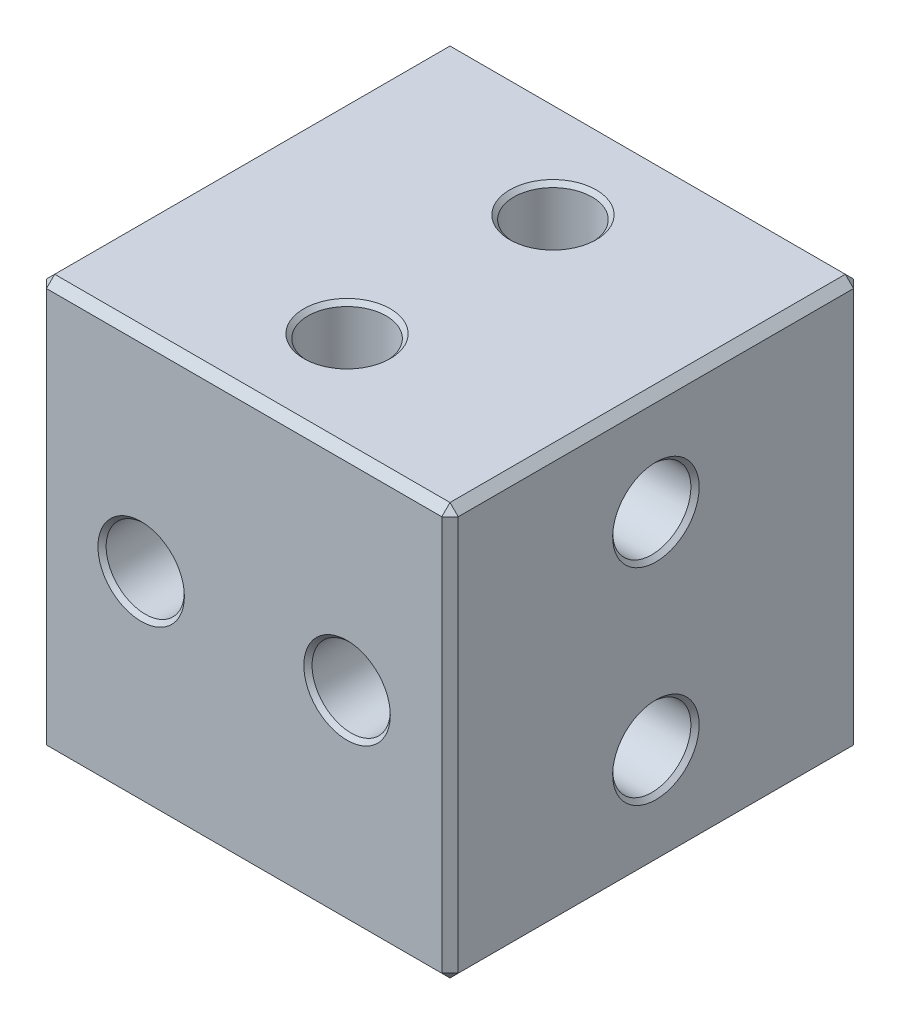
SolidWorks part; units mm, degrees
ref_plane "Front Plane" through (0, 0, 0) normal (0, 0, 1) x (1, 0, 0)
ref_plane "Top Plane" through (0, 0, 0) normal (0, 1, 0) x (1, 0, 0)
ref_plane "Right Plane" through (0, 0, 0) normal (1, 0, 0) x (0, 0, -1)
sketch "Sketch1" plane through (0, 0, 0) normal (0, 0, 1) x (1, 0, 0)
  line L0 (0, 38.089) -> (0, -37.1739) construction
  line L1 (-5, 5) -> (5, -5) construction
  line L2 (-5, 5) -> (5, 5)
  line L3 (-5, 5) -> (-5, -5)
  line L4 (-5, -5) -> (5, -5)
  line L5 (5, 5) -> (5, -5)
  line L6 (5, 5) -> (-5, -5) construction
  dimension "D1" = 10
  dimension "D2" = 10
extrude "Boss-Extrude1" add sketch "Sketch1" along normal blind 10
sketch "Sketch2" plane through (0, 0, 10) normal (0, 0, 1) x (1, 0, 0)
  line L0 (0, 6.9914) -> (0, -10.1171) construction
  circle A0 centre (-2.5, 0) radius 0.95
  circle A1 centre (2.5, 0) radius 0.95
  point P7 (0, 0)
  dimension "D2" = 5
extrude "Cut-Extrude1" cut sketch "Sketch2" against normal through all
cosmetic thread "Cosmetic Thread19" parameters "D2"=2
cosmetic thread "Cosmetic Thread20" parameters "D2"=2
cosmetic thread "Cosmetic Thread25" parameters "D2"=2
cosmetic thread "Cosmetic Thread26" parameters "D2"=2
sketch "Sketch3" plane through (0, 5, 0) normal (0, 1, 0) x (1, 0, 0)
  line L0 (5.3801, -5) -> (-5.5778, -5) construction
  line L1 (5, 0) -> (-5, -10) construction
  line L2 (5, -10) -> (-5, 0) construction
  circle A0 centre (0, -7.5) radius 0.95
  circle A1 centre (0, -2.5) radius 0.95
  point P2 (0, -5)
  dimension "D1" = 5
extrude "Cut-Extrude2" cut sketch "Sketch3" against normal through all
cosmetic thread "Cosmetic Thread15" parameters "D2"=2
cosmetic thread "Cosmetic Thread16" parameters "D2"=2
cosmetic thread "Cosmetic Thread23" parameters "D2"=2
cosmetic thread "Cosmetic Thread24" parameters "D2"=2
sketch "Sketch5" plane through (5, 0, 0) normal (1, 0, 0) x (0, 0, -1)
  line L0 (2.556, 0) -> (-10.2927, 0) construction
  line L2 (0, -5) -> (-10, 5) construction
  line L3 (-10, -5) -> (0, 5) construction
  circle A0 centre (-5, 2.5) radius 0.95
  circle A1 centre (-5, -2.5) radius 0.95
  point P15 (-5, 0)
  dimension "D2" = 5
extrude "Cut-Extrude4" cut sketch "Sketch5" against normal through all
cosmetic thread "Cosmetic Thread17" parameters "D2"=2
cosmetic thread "Cosmetic Thread18" parameters "D2"=2
cosmetic thread "Cosmetic Thread21" parameters "D2"=2
cosmetic thread "Cosmetic Thread22" parameters "D2"=2
chamfer "Chamfer1" distance 0.2 distance2 0.2 12 edges at (0, -5, 10) (-5, -5, 5) (-5, 0, 10) (5, 0, 10) (5, -5, 5) (0, -5, 0) (5, 0, 0) (-5, 0, 0) (-5, 5, 5) (0, 5, 10) (5, 5, 5) (0, 5, 0)
chamfer "Chamfer2" distance 0.1 distance2 0.1 12 edges at (-1.55, 0, 0) (1.55, 0, 0) (-1.55, 0, 10) (1.55, 0, 10) (0, 5, 3.45) (0, 5, 6.55) (-5, -3.45, 5) (-5, 3.45, 5) (0, -5, 3.45) (0, -5, 6.55) (5, 3.45, 5) (5, -3.45, 5)
